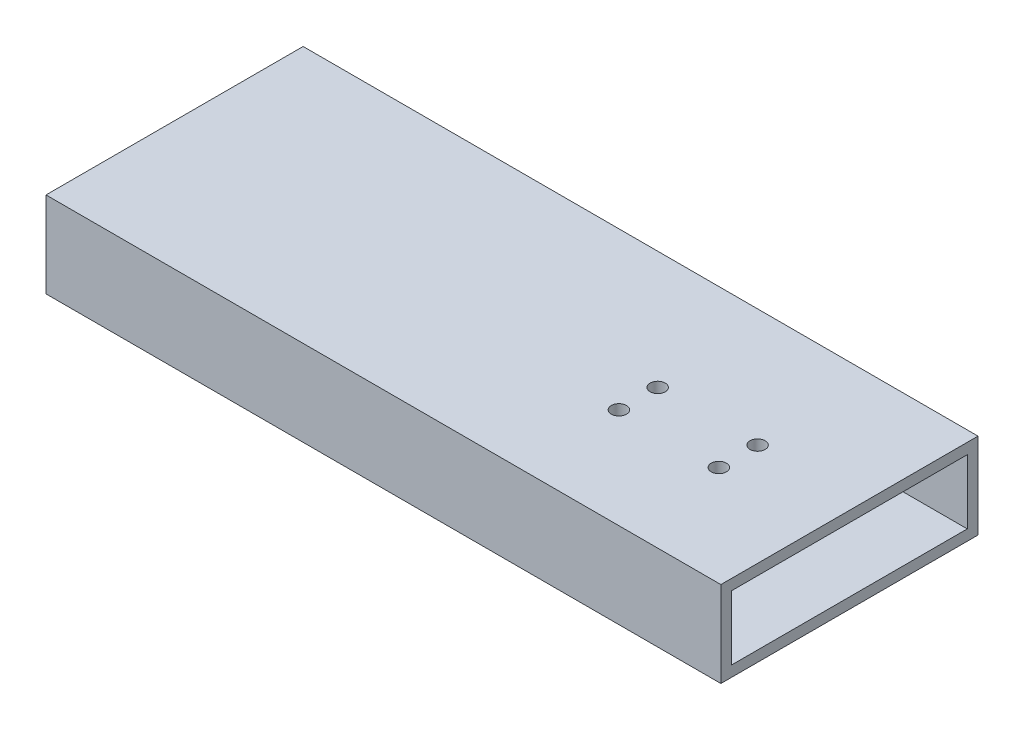
SolidWorks part; units mm, degrees
ref_plane "Front Plane" through (0, 0, 0) normal (0, 0, 1) x (1, 0, 0)
ref_plane "Top Plane" through (0, 0, 0) normal (0, 1, 0) x (1, 0, 0)
ref_plane "Right Plane" through (0, 0, 0) normal (1, 0, 0) x (0, 0, -1)
sketch "Sketch1" plane through (0, 0, 0) normal (1, 0, 0) x (0, 0, -1)
  line L1 (-76.2, -25.4) -> (76.2, -25.4)
  line L2 (-76.2, -25.4) -> (-76.2, 25.4)
  line L3 (-76.2, 25.4) -> (76.2, 25.4)
  line L4 (76.2, -25.4) -> (76.2, 25.4)
  line L5 (-76.2, -25.4) -> (76.2, 25.4) construction
  line L6 (-76.2, 25.4) -> (76.2, -25.4) construction
  line L7 (-69.85, -19.05) -> (69.85, -19.05)
  line L8 (-69.85, -19.05) -> (-69.85, 19.05)
  line L9 (-69.85, 19.05) -> (69.85, 19.05)
  line L10 (69.85, -19.05) -> (69.85, 19.05)
  line L11 (-69.85, -19.05) -> (69.85, 19.05) construction
  line L12 (-69.85, 19.05) -> (69.85, -19.05) construction
  point P1 (0, 0)
  point P6 (0, 0)
  dimension "D1" = 152.4
  dimension "D2" = 50.8
  dimension "D3" = 6.35
  dimension "D4" = 6.35
extrude "Boss-Extrude1" add sketch "Sketch1" along normal blind 400
sketch "Sketch2" plane through (0, 0, 76.2) normal (0, 0, 1) x (1, 0, 0)
  line L0 (314.3619, -160.5625) -> (314.3619, 25.4) construction
  line L1 (400, 25.4) -> (0, 25.4) construction
  line L2 (400, -25.4) -> (0, -25.4) construction
  line L3 (400, -25.4) -> (0, -25.4)
sketch "Sketch4" plane through (0, -25.4, 0) normal (0, -1, 0) x (1, 0, 0)
  line L0 (309.69, 76.2) -> (309.69, -76.2) construction
  line L1 (400, 76.2) -> (0, 76.2) construction
  line L2 (400, -76.2) -> (0, -76.2) construction
  line L3 (0, 76.2) -> (0, -76.2) construction
  dimension "D1" = 309.69
sketch "Sketch5" plane through (0, -25.4, 0) normal (0, -1, 0) x (1, 0, 0)
  line L1 (280.09, -6.27) -> (339.29, -6.27)
  line L2 (280.09, -6.27) -> (280.09, 16.73)
  line L3 (280.09, 16.73) -> (339.29, 16.73)
  line L4 (339.29, -6.27) -> (339.29, 16.73)
hole_wizard "M8 Clearance Hole1" positions "Sketch7" profile "Sketch6" hole size "M8" standard "ANSI Metric" end condition through all
sketch "Sketch7" plane through (0, -25.4, 0) normal (0, -1, 0) x (-1, 0, 0)
  point P0 (-280.09, -16.73)
  point P3 (-280.09, 6.27)
  point P6 (-339.29, 6.27)
  point P9 (-339.29, -16.73)
sketch "Sketch6" plane through (280.09, -25.4, 16.73) normal (1, 0, 0) x (0, 0, -1)
  line L0 (0, 0) -> (0, 50.8)
  line L1 (0, 50.8) -> (4.5, 50.8)
  line L2 (4.5, 50.8) -> (4.5, 0)
  line L5 (4.5, 0) -> (0, 0)
  line L11 (0, -6.35) -> (0, 107.95) construction
  dimension "Thru Hole Dia." = 9
  dimension "Thru Hole Depth" = 50.8
